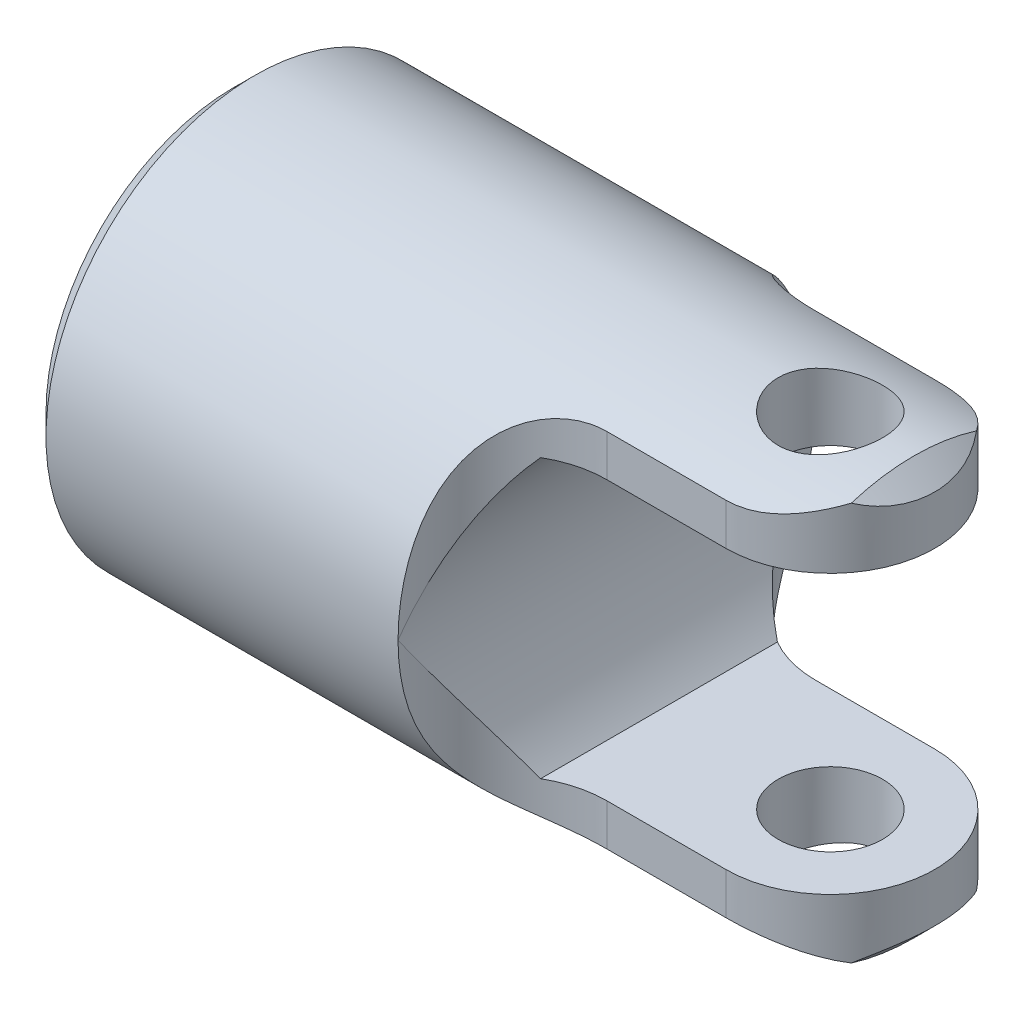
SolidWorks part; units mm, degrees
material "AISI 1045 Steel, cold drawn"
ref_plane "Front Plane" through (0, 0, 0) normal (0, 0, 1) x (1, 0, 0)
ref_plane "Top Plane" through (0, 0, 0) normal (0, 1, 0) x (1, 0, 0)
ref_plane "Right Plane" through (0, 0, 0) normal (1, 0, 0) x (0, 0, -1)
sketch "Sketch0" plane through (0, 0, 0) normal (0, 1, 0) x (1, 0, 0)
  line L0 (-63.5, 0) -> (63.5, 0) construction
  line L1 (-63.5, 22.225) -> (-63.5, -22.225) construction
  line L2 (-23.8125, 3.175) -> (-23.8125, -3.175) construction
  line L3 (-23.8125, 3.175) -> (-20.6375, 0) construction
  line L4 (-20.6375, 0) -> (-23.8125, -3.175) construction
  line L5 (-22.225, 1.5875) -> (-22.225, -1.5875) construction
  point P7 (-23.8125, 0)
  point P8 (0, 0)
  point P12 (-22.225, 0)
  dimension "D1" = 6.35
sketch "Sketch1" plane through (0, 0, 0) normal (0, 1, 0) x (1, 0, 0)
  line L0 (-63.5, 22.225) -> (-23.0188, 22.225)
  line L1 (11.1125, 22.225) -> (11.1125, 0)
  line L2 (11.1125, 0) -> (-63.5, 0)
  line L3 (-63.5, 0) -> (-63.5, 22.225)
  line L4 (-63.5, 22.225) -> (-63.5, -22.225) construction
  line L5 (-63.5, 0) -> (63.5, 0) construction
  line L6 (-23.0188, 22.225) -> (11.1125, 22.225)
  line L7 (-23.0188, 1.5875) -> (-23.0188, 22.225) construction
  line L11 (0, 0) -> (22.225, 0) construction
  line L12 (-22.225, 1.5875) -> (-23.8125, 1.5875) construction
  line L13 (-23.8125, 3.175) -> (-23.8125, -3.175) construction
  circle A0 centre (0, 0) radius 22.225 construction
  dimension "D3" = 74.6125
revolve "Revolve1" add sketch "Sketch1" angle 360 about L0
chamfer "Chamfer1" distance 2.2225 angle 45 2 edges at (-63.5, 0, 22.225) (11.1125, 0, 22.225)
sketch "Sketch2" plane through (0, 0, 0) normal (0, 1, 0) x (1, 0, 0)
  line L0 (-61.2775, 22.225) -> (-23.7998, 22.225) construction
  line L1 (-23.0188, 22.225) -> (11.1125, 22.225) construction
  line L2 (8.89, 22.225) -> (-61.2775, 22.225) construction
  line L4 (-63.5, 0) -> (11.1125, 0) construction
  line L5 (-23.7998, 22.225) -> (22.225, 22.225)
  line L6 (22.225, 22.225) -> (22.225, -22.225)
  line L7 (22.225, -22.225) -> (-23.7998, -22.225)
  line L8 (0, 11.1125) -> (0, 0) construction
  line L9 (0, 11.1125) -> (-12.6873, 11.1125)
  line L10 (-23.7998, 22.225) -> (-23.7998, -22.225) construction
  line L11 (0, -11.1125) -> (-12.6873, -11.1125)
  arc A0 (-23.7998, 22.225) -> (-12.6873, 11.1125) centre (-12.6873, 22.225) ccw
  arc A1 (0, -11.1125) -> (0, 11.1125) centre (0, 0) ccw
  arc A2 (-12.6873, -11.1125) -> (-23.7998, -22.225) centre (-12.6873, -22.225) ccw
  dimension "D1" = 22.225
  dimension "D" = 39.7002
extrude "Extrude1" cut sketch "Sketch2" against normal through all and the other way through all
sketch "Sketch3" plane through (0, 0, 0) normal (0, 0, 1) x (1, 0, 0)
  line L0 (-18.2436, 14.8019) -> (-23.7998, 9.2456) construction
  line L1 (-18.2436, 14.8019) -> (22.225, 14.8018)
  line L2 (-23.7998, 9.2456) -> (-23.7998, -9.2456) construction
  line L3 (-18.2436, -14.8019) -> (22.225, -14.8018)
  line L4 (22.225, 14.8018) -> (22.225, -14.8018)
  line L5 (-23.7998, -9.2456) -> (-18.2436, -14.8019) construction
  line L6 (-23.7998, 0) -> (-12.6873, 0) construction
  line L7 (-12.6873, -19.2474) -> (-12.6873, 19.2474) construction
  line L8 (22.225, 0) -> (-23.7998, 0) construction
  line L9 (-18.2436, 0) -> (-18.2436, 14.8019) construction
  arc A0 (-18.2436, 14.8019) -> (-18.2436, -14.8019) centre (-1.3056, 0) ccw
  dimension "D1" = 29.6037
extrude "Extrude3" cut sketch "Sketch3" against normal through all and the other way through all
sketch "Sketch4" plane through (-63.5, 0, 0) normal (-1, 0, 0) x (0, 0, 1)
  circle A0 centre (0, 0) radius 3.175
  circle A1 centre (0, 0) radius 12.7 construction
  dimension "Max Bore Dia" = 25.4
extrude "Extrude4" cut sketch "Sketch4" against normal blind 6.35
sketch "Sketch5" plane through (-57.15, 0, 0) normal (-1, 0, 0) x (0, 0, 1)
  circle A0 centre (0, 0) radius 3.175 construction
  circle A1 centre (0, 0) radius 3.175
extrude "Extrude5" cut sketch "Sketch5" against normal through all draft 45
sketch "Sketch6" plane through (0, 0, 0) normal (0, 1, 0) x (1, 0, 0)
  line L0 (-63.5, 0) -> (63.5, 0) construction
  line L1 (11.1125, 0) -> (5.5562, 0) construction
  line L2 (5.5562, 0) -> (0, 0) construction
  circle A0 centre (0, 0) radius 5.5562
  arc A1 (0, -11.1125) -> (0, 11.1125) centre (0, 0) ccw construction
  dimension "D1" = 11.1125
extrude "Extrude6" cut sketch "Sketch6" against normal through all and the other way through all
equation "\"D2@Sketch3\" = \"D1@Sketch3\" / 4"
equation "\"D1@Sketch3\" = \"OD@Sketch0\"*.666"
equation "\"D1@Chamfer1\" = \"OD@Sketch0\"/20"
